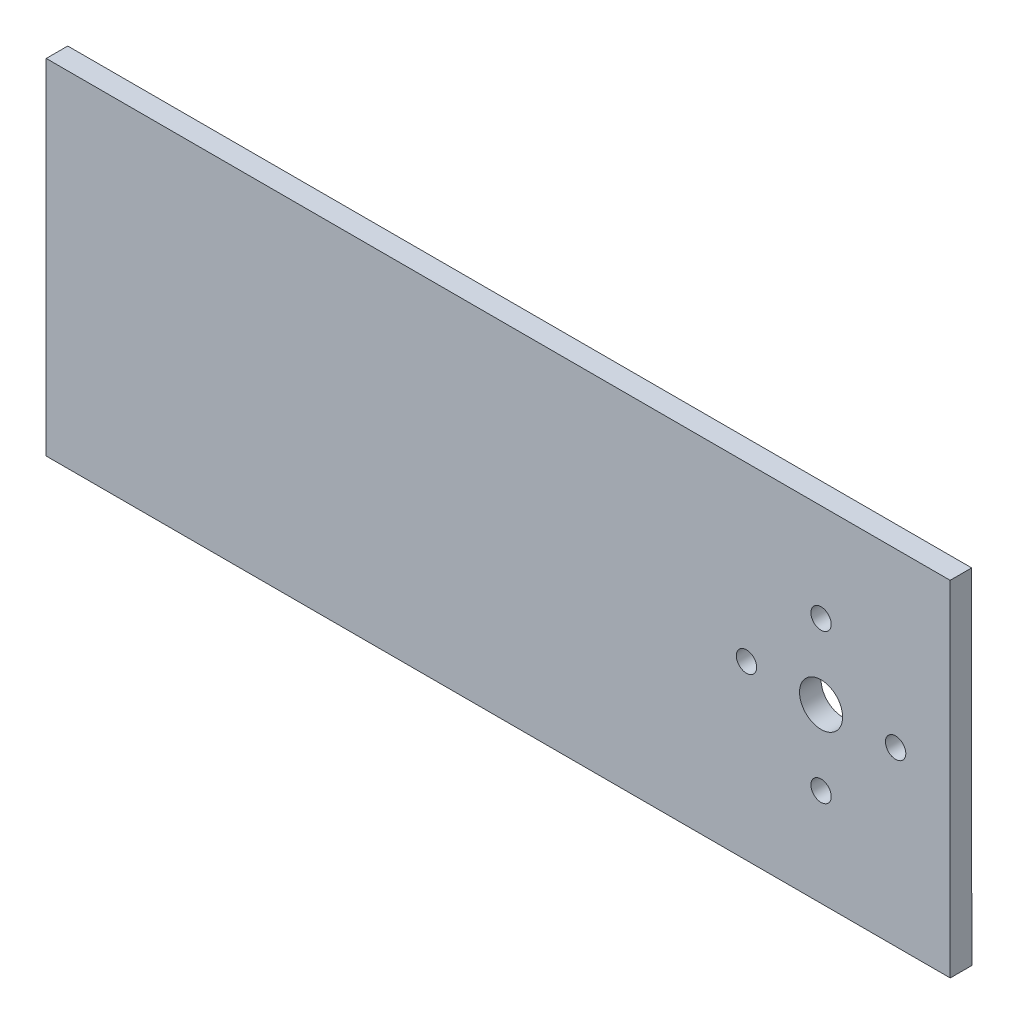
SolidWorks part; units mm, degrees
material "6061-T6 (SS)"
ref_plane "Front Plane" through (0, 0, 0) normal (0, 0, 1) x (1, 0, 0)
ref_plane "Top Plane" through (0, 0, 0) normal (0, 1, 0) x (1, 0, 0)
ref_plane "Right Plane" through (0, 0, 0) normal (1, 0, 0) x (0, 0, -1)
ref_plane "Plane1" through (0, 0, 50.8) normal (0, 0, 1) x (1, 0, 0)
sketch "Sketch1" plane through (0, 0, 50.8) normal (0, 0, 1) x (1, 0, 0)
  line L1 (0, 0) -> (101.6, 0) construction
  line L4 (101.6, 15.875) -> (101.6, -15.875) construction
  line L5 (0, 25.4) -> (-12.7, 25.4)
  line L6 (-12.7, 25.4) -> (-12.7, -25.4)
  line L7 (-12.7, -25.4) -> (0, -25.4)
  line L8 (0, 25.4) -> (120.6424, 25.4)
  line L9 (0, -25.4) -> (120.6576, -25.4)
  line L10 (120.6424, 25.4) -> (120.6576, -25.4)
  circle A0 centre (101.6, 0) radius 3.175
  circle A2 centre (101.6, 0) radius 11 construction
  circle A3 centre (101.6, 11) radius 1.5
  circle A4 centre (112.6, 0) radius 1.5
  circle A5 centre (101.6, -11) radius 1.5
  circle A6 centre (90.6, 0) radius 1.5
  point P1 (-12.7, 0)
  point P4 (0, 0)
  dimension "D3" = 6.35
  dimension "D7" = 22
  dimension "D8" = 3
  dimension "D1" = 50.8
  dimension "D2" = 101.6
  dimension "D5" = 12.7
  dimension "D6" = 12.7
  dimension "D4" = 19.05
extrude "Boss-Extrude1" add sketch "Sketch1" along normal blind 3.175
sketch "Sketch2" plane through (0, 0, 0) normal (0, 0, 1) x (1, 0, 0)
  line L0 (0, 25.4) -> (0, -25.4) construction
  point P3 (0, 0)
  dimension "D1" = 50.8
equation "\"HeightOfTubing\"=2"
equation "\"D1@Sketch1\"=\"HeightOfTubing\""
equation "\"D1@Sketch2\"=\"HeightOfTubing\""
